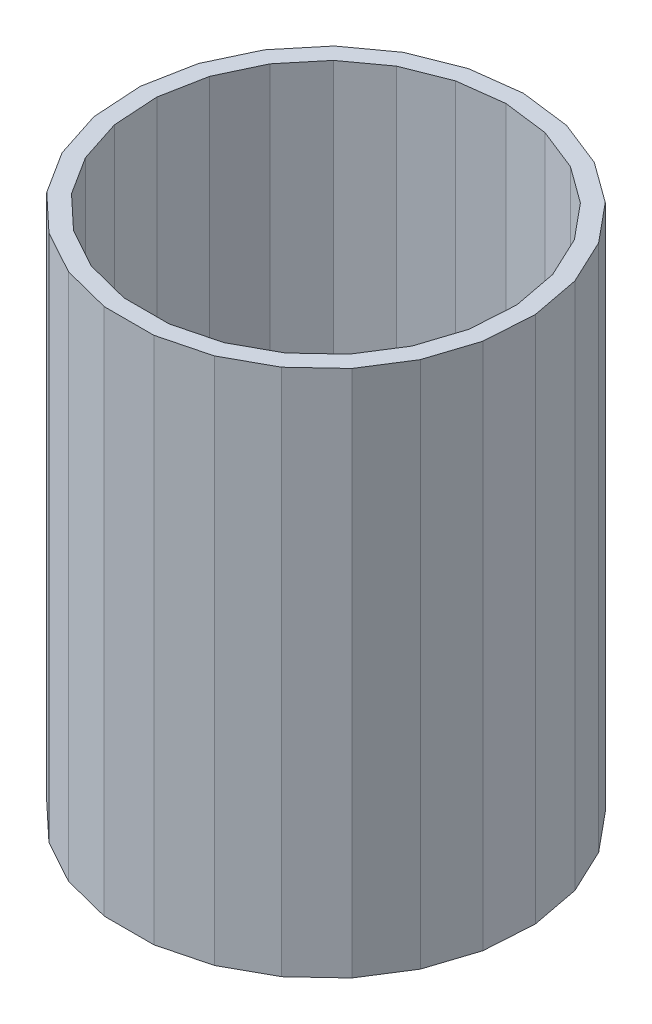
SolidWorks part; units mm, degrees
ref_plane "Front Plane" through (0, 0, 0) normal (0, 0, 1) x (1, 0, 0)
ref_plane "Top Plane" through (0, 0, 0) normal (0, 1, 0) x (1, 0, 0)
ref_plane "Right Plane" through (0, 0, 0) normal (1, 0, 0) x (0, 0, -1)
sketch "Sketch2" plane through (0, 0, 0) normal (0, 1, 0) x (1, 0, 0)
  line L1 (0, 57.15) -> (-14.2126, 55.3545)
  line L2 (-14.2126, 55.3545) -> (-27.5322, 50.0809)
  line L3 (-27.5322, 50.0809) -> (-39.1219, 41.6606)
  line L4 (-39.1219, 41.6606) -> (-48.2533, 30.6225)
  line L5 (-48.2533, 30.6225) -> (-54.3529, 17.6603)
  line L6 (-54.3529, 17.6603) -> (-57.0372, 3.5885)
  line L7 (-57.0372, 3.5885) -> (-56.1377, -10.7088)
  line L8 (-56.1377, -10.7088) -> (-51.7109, -24.3333)
  line L9 (-51.7109, -24.3333) -> (-44.0348, -36.4288)
  line L10 (-44.0348, -36.4288) -> (-33.5919, -46.2353)
  line L11 (-33.5919, -46.2353) -> (-21.0383, -53.1367)
  line L12 (-21.0383, -53.1367) -> (-7.1628, -56.6994)
  line L13 (-7.1628, -56.6994) -> (7.1628, -56.6994)
  line L14 (7.1628, -56.6994) -> (21.0383, -53.1367)
  line L15 (21.0383, -53.1367) -> (33.5919, -46.2353)
  line L16 (33.5919, -46.2353) -> (44.0348, -36.4288)
  line L17 (44.0348, -36.4288) -> (51.7109, -24.3333)
  line L18 (51.7109, -24.3333) -> (56.1377, -10.7088)
  line L19 (56.1377, -10.7088) -> (57.0372, 3.5885)
  line L20 (57.0372, 3.5885) -> (54.3529, 17.6603)
  line L21 (54.3529, 17.6603) -> (48.2533, 30.6225)
  line L22 (48.2533, 30.6225) -> (39.1219, 41.6606)
  line L23 (39.1219, 41.6606) -> (27.5322, 50.0809)
  line L24 (27.5322, 50.0809) -> (14.2126, 55.3545)
  line L25 (14.2126, 55.3545) -> (0, 57.15)
  line L26 (0, 52.07) -> (-12.9493, 50.4341)
  line L27 (-12.9493, 50.4341) -> (-25.0849, 45.6293)
  line L28 (-25.0849, 45.6293) -> (-35.6444, 37.9574)
  line L29 (-35.6444, 37.9574) -> (-43.9642, 27.9005)
  line L30 (-43.9642, 27.9005) -> (-49.5215, 16.0905)
  line L31 (-49.5215, 16.0905) -> (-51.9673, 3.2695)
  line L32 (-51.9673, 3.2695) -> (-51.1477, -9.7569)
  line L33 (-51.1477, -9.7569) -> (-47.1143, -22.1703)
  line L34 (-47.1143, -22.1703) -> (-40.1206, -33.1907)
  line L35 (-40.1206, -33.1907) -> (-30.606, -42.1255)
  line L36 (-30.606, -42.1255) -> (-19.1682, -48.4135)
  line L37 (-19.1682, -48.4135) -> (-6.5261, -51.6594)
  line L38 (-6.5261, -51.6594) -> (6.5261, -51.6594)
  line L39 (6.5261, -51.6594) -> (19.1682, -48.4135)
  line L40 (19.1682, -48.4135) -> (30.606, -42.1255)
  line L41 (30.606, -42.1255) -> (40.1206, -33.1907)
  line L42 (40.1206, -33.1907) -> (47.1143, -22.1703)
  line L43 (47.1143, -22.1703) -> (51.1477, -9.7569)
  line L44 (51.1477, -9.7569) -> (51.9673, 3.2695)
  line L45 (51.9673, 3.2695) -> (49.5215, 16.0905)
  line L46 (49.5215, 16.0905) -> (43.9642, 27.9005)
  line L47 (43.9642, 27.9005) -> (35.6444, 37.9574)
  line L48 (35.6444, 37.9574) -> (25.0849, 45.6293)
  line L49 (25.0849, 45.6293) -> (12.9493, 50.4341)
  line L50 (12.9493, 50.4341) -> (0, 52.07)
  circle A0 centre (0, 0) radius 57.15 construction
  circle A1 centre (0, 0) radius 52.07 construction
  dimension "D1" = 5.08
  dimension "D2" = 52.07
extrude "Boss-Extrude1" add sketch "Sketch2" along normal blind 152.4
equation "\"GMaterial\" = 0.21in"
equation "\"MDF\"= 0.21in"
equation "\"Foamcore\"= 0.2in"
equation "\"D1@Sketch2\"=\"Foamcore\""
equation "\"D2@Sketch2\"=2.25-\"Foamcore\""
